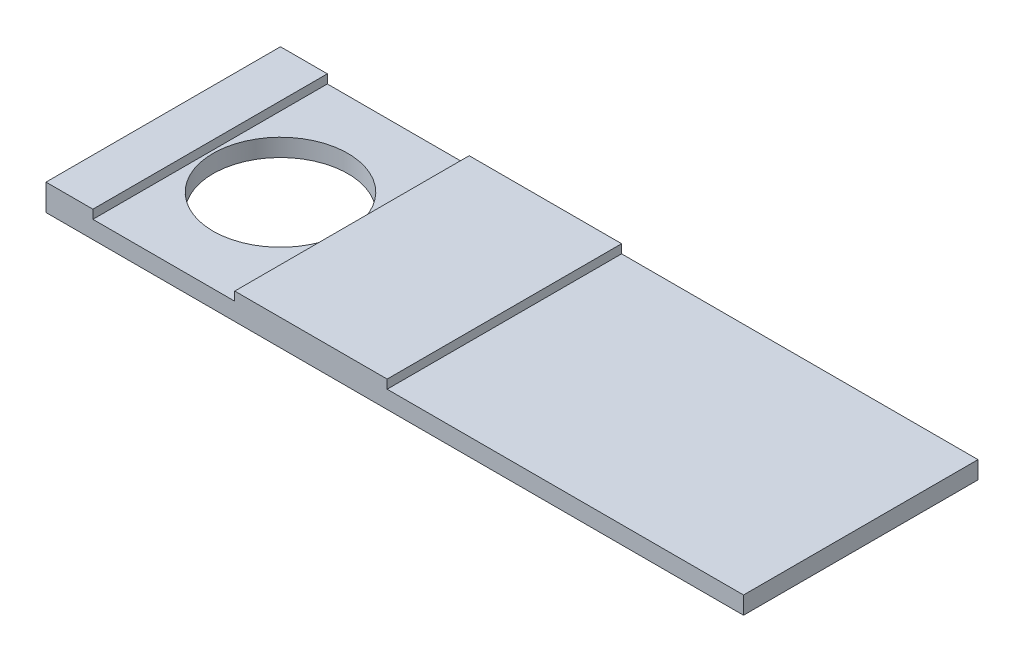
SolidWorks part; units mm, degrees
ref_plane "Front Plane" through (0, 0, 0) normal (0, 0, 1) x (1, 0, 0)
ref_plane "Top Plane" through (0, 0, 0) normal (0, 1, 0) x (1, 0, 0)
ref_plane "Right Plane" through (0, 0, 0) normal (1, 0, 0) x (0, 0, -1)
sketch "Sketch1" plane through (0, 0, 0) normal (0, 1, 0) x (1, 0, 0)
  line L1 (-59.5, -20) -> (59.5, -20)
  line L2 (-59.5, -20) -> (-59.5, 20)
  line L3 (-59.5, 20) -> (59.5, 20)
  line L4 (59.5, -20) -> (59.5, 20)
  line L5 (-59.5, -20) -> (59.5, 20) construction
  line L6 (-59.5, 20) -> (59.5, -20) construction
  circle A0 centre (-39.5, 0) radius 11.5
  point P0 (0, 0)
  dimension "D5" = 23
  dimension "D1" = 119
  dimension "D2" = 40
  dimension "D3" = 20
  dimension "D4" = 20
extrude "Boss-Extrude1" add sketch "Sketch1" along normal blind 3
sketch "Sketch2" plane through (0, 3, 0) normal (0, 1, 0) x (1, 0, 0)
  line L0 (59.5, 20) -> (-59.5, 20) construction
  line L1 (-27.3, 20) -> (-1.3, 20)
  line L2 (-27.3, 20) -> (-27.3, -20)
  line L3 (-27.3, -20) -> (-1.3, -20)
  line L4 (-1.3, 20) -> (-1.3, -20)
  line L5 (-59.5, -20) -> (59.5, -20) construction
  line L7 (-59.5, 20) -> (-51.5, 20)
  line L8 (-59.5, 20) -> (-59.5, -20)
  line L9 (-59.5, -20) -> (-51.5, -20)
  line L10 (-51.5, 20) -> (-51.5, -20)
  dimension "D1" = 26
  dimension "D2" = 8
  dimension "D4" = 58.2
extrude "Boss-Extrude2" add sketch "Sketch2" along normal blind 1.5
